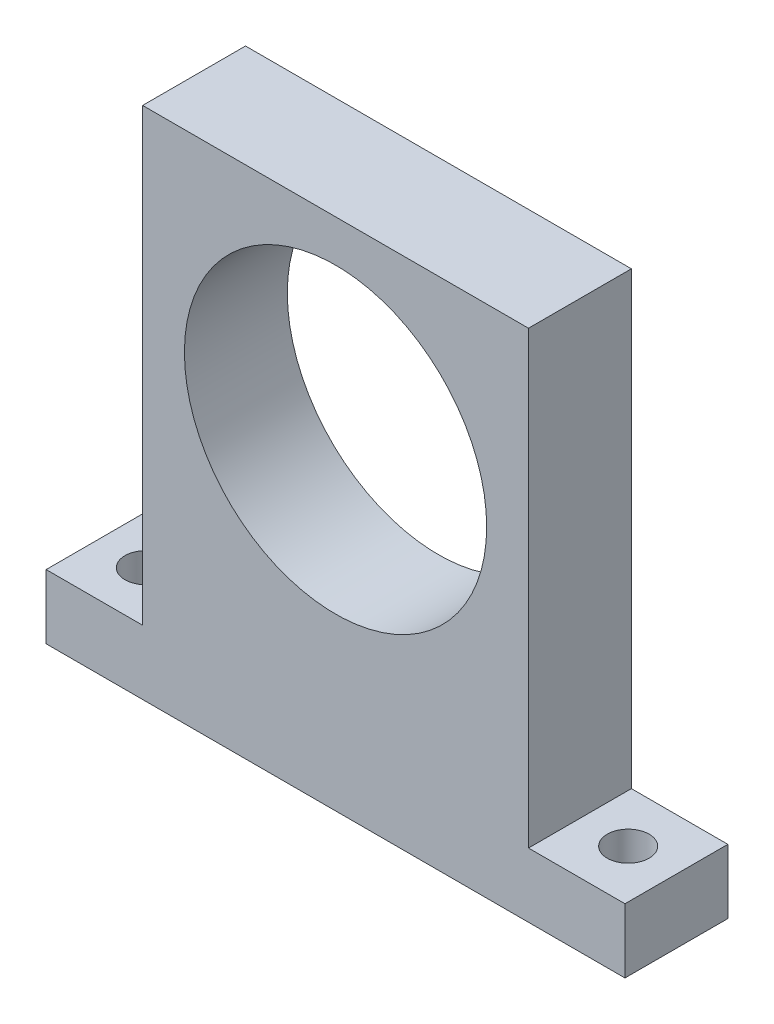
SolidWorks part; units mm, degrees
ref_plane "Front Plane" through (0, 0, 0) normal (0, 0, 1) x (1, 0, 0)
ref_plane "Top Plane" through (0, 0, 0) normal (0, 1, 0) x (1, 0, 0)
ref_plane "Right Plane" through (0, 0, 0) normal (1, 0, 0) x (0, 0, -1)
sketch "Sketch1" plane through (0, 0, 0) normal (0, 0, 1) x (1, 0, 0)
  line L1 (-30, -40) -> (30, -40)
  line L2 (-30, -40) -> (-30, 40)
  line L3 (-30, 40) -> (30, 40)
  line L4 (30, -40) -> (30, 40)
  line L5 (0, 40) -> (0, -40) construction
  line L6 (-30, 0) -> (30, 0) construction
  circle A0 centre (0, 10) radius 23.5
  point P0 (0, 0)
  dimension "D3" = 47
  dimension "D4" = 30
  dimension "D1" = 60
  dimension "D2" = 80
extrude "Boss-Extrude1" add sketch "Sketch1" along normal mid plane 16
sketch "Sketch2" plane through (0, -40, 0) normal (0, -1, 0) x (1, 0, 0)
  line L0 (-30, -8) -> (30, -8) construction
  line L1 (30, 8) -> (45, 8)
  line L2 (30, 8) -> (30, -8)
  line L3 (30, -8) -> (45, -8)
  line L4 (45, 8) -> (45, -8)
  line L5 (37.5, -8) -> (37.5, 8) construction
  line L6 (30, 0) -> (45, 0) construction
  circle A0 centre (37.5, 0) radius 3.25
  point P776 (37.5, 0)
  dimension "D2" = 6.5
  dimension "D1" = 15
extrude "Boss-Extrude2" add sketch "Sketch2" against normal blind 10
mirror "Mirror1" about plane through (0, 0, 0) normal (1, 0, 0) of "Boss-Extrude2"
